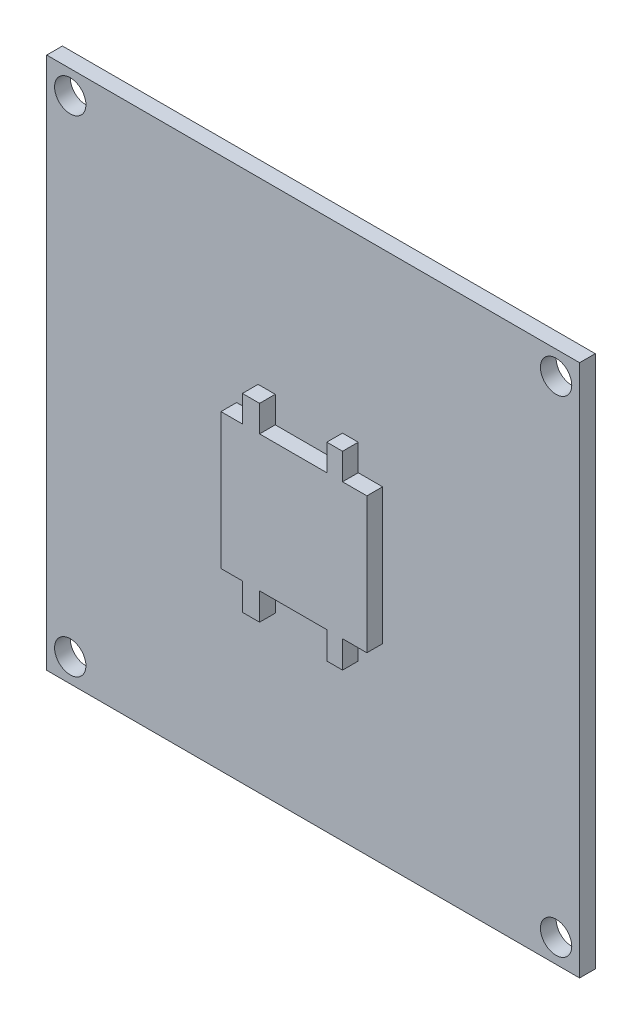
SolidWorks part; units mm, degrees
ref_plane "Alzado" through (0, 0, 0) normal (0, 0, 1) x (1, 0, 0)
ref_plane "Planta" through (0, 0, 0) normal (0, 1, 0) x (1, 0, 0)
ref_plane "Vista lateral" through (0, 0, 0) normal (1, 0, 0) x (0, 0, -1)
sketch "Croquis1" plane through (0, 0, 0) normal (0, 0, 1) x (1, 0, 0)
  line L0 (1.5, 32.5) -> (32.5, 32.5) construction
  line L1 (0, 0) -> (34, 0)
  line L2 (0, 0) -> (0, 34)
  line L3 (0, 34) -> (34, 34)
  line L4 (34, 0) -> (34, 34)
  line L5 (1.5, 32.5) -> (1.5, 1.5) construction
  line L6 (1.5, 1.5) -> (32.5, 1.5) construction
  line L7 (32.5, 1.5) -> (32.5, 32.5) construction
  circle A0 centre (1.5, 32.5) radius 1
  circle A1 centre (32.5, 32.5) radius 1
  circle A2 centre (1.5, 1.5) radius 1
  circle A3 centre (32.5, 1.5) radius 1
  dimension "D3" = 2
  dimension "D8" = 2
  dimension "D1" = 34
  dimension "D2" = 34
  dimension "D4" = 31
  dimension "D5" = 1.5
  dimension "D6" = 31
  dimension "D7" = 1.5
extrude "Saliente-Extruir1" add sketch "Croquis1" along normal blind 1
sketch "Croquis2" plane through (0, 0, 1) normal (0, 0, 1) x (1, 0, 0)
  line L1 (21.4272, 20.8566) -> (12.1164, 20.8566)
  line L2 (21.4272, 20.8566) -> (21.4272, 12.1849)
  line L3 (21.4272, 12.1849) -> (12.1164, 12.1849)
  line L4 (12.1164, 20.8566) -> (12.1164, 12.1849)
  line L5 (13.4857, 20.8566) -> (14.581, 20.8566)
  line L6 (13.4857, 20.8566) -> (13.4857, 22.5454)
  line L7 (13.4857, 22.5454) -> (14.581, 22.5454)
  line L8 (14.581, 20.8566) -> (14.581, 22.5454)
  line L9 (18.8713, 20.8566) -> (19.8754, 20.8566)
  line L10 (18.8713, 20.8566) -> (18.8713, 22.5454)
  line L11 (18.8713, 22.5454) -> (19.8754, 22.5454)
  line L12 (19.8754, 20.8566) -> (19.8754, 22.5454)
  line L13 (13.4857, 12.1849) -> (14.581, 12.1849)
  line L14 (13.4857, 12.1849) -> (13.4857, 10.4505)
  line L15 (13.4857, 10.4505) -> (14.581, 10.4505)
  line L16 (14.581, 12.1849) -> (14.581, 10.4505)
  line L17 (18.8713, 12.1849) -> (19.8754, 12.1849)
  line L18 (18.8713, 12.1849) -> (18.8713, 10.4505)
  line L19 (18.8713, 10.4505) -> (19.8754, 10.4505)
  line L20 (19.8754, 12.1849) -> (19.8754, 10.4505)
extrude "Saliente-Extruir2" add sketch "Croquis2" along normal blind 1 contours L1 L4 L3 L2 | L1 L8 L7 L6 | L1 L12 L11 L10 | L16 L3 L14 L15 | L20 L3 L18 L19
